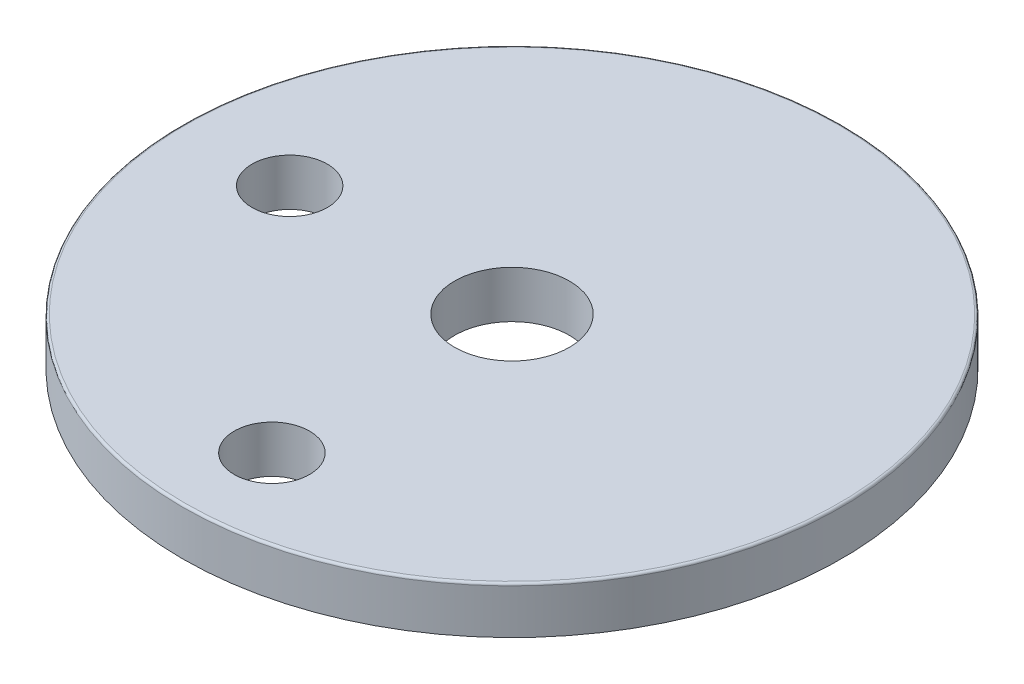
SolidWorks part; units mm, degrees
ref_plane "Front Plane" through (0, 0, 0) normal (0, 0, 1) x (1, 0, 0)
ref_plane "Top Plane" through (0, 0, 0) normal (0, 1, 0) x (1, 0, 0)
ref_plane "Right Plane" through (0, 0, 0) normal (1, 0, 0) x (0, 0, -1)
sketch "Sketch1" plane through (0, 0, 0) normal (0, 1, 0) x (1, 0, 0)
  line L0 (-23.61, 0) -> (0, 0) construction
  line L1 (0, 0) -> (0, -25.5) construction
  circle A0 centre (0, 0) radius 6.1
  circle A1 centre (0, 0) radius 35
  circle A2 centre (-23.61, 0) radius 4
  circle A3 centre (0, -25.5) radius 4
  dimension "D1" = 23.61
extrude "Boss-Extrude2" add sketch "Sketch1" along normal blind 5
fillet "Fillet1" radius 0.25 1 edges at (0, 5, 35)
